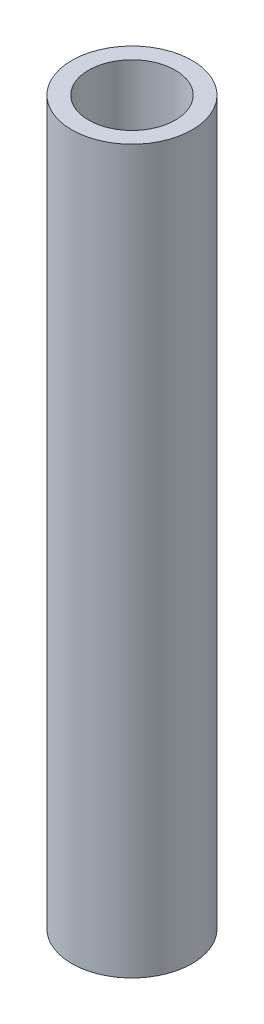
SolidWorks part; units mm, degrees
material "AISI 316 Stainless Steel Sheet (SS)"
ref_plane "Front Plane" through (0, 0, 0) normal (0, 0, 1) x (1, 0, 0)
ref_plane "Top Plane" through (0, 0, 0) normal (0, 1, 0) x (1, 0, 0)
ref_plane "Right Plane" through (0, 0, 0) normal (1, 0, 0) x (0, 0, -1)
sketch "Sketch1" plane through (0, 0, 0) normal (0, 1, 0) x (1, 0, 0)
  circle A0 centre (0, 0) radius 3.175
  circle A1 centre (0, 0) radius 2.286
  dimension "D1" = 6.35
  dimension "D2" = 4.572
extrude "Boss-Extrude1" add sketch "Sketch1" along normal blind 38.1
